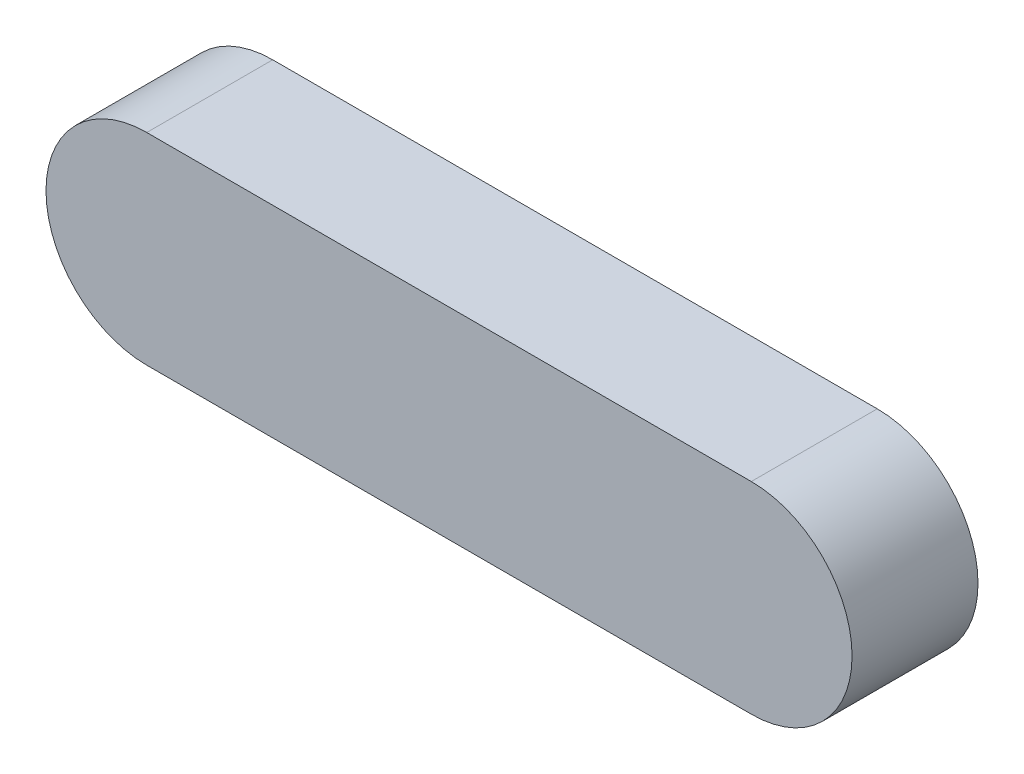
SolidWorks part; units mm, degrees
ref_plane "Front Plane" through (0, 0, 0) normal (0, 0, 1) x (1, 0, 0)
ref_plane "Top Plane" through (0, 0, 0) normal (0, 1, 0) x (1, 0, 0)
ref_plane "Right Plane" through (0, 0, 0) normal (1, 0, 0) x (0, 0, -1)
sketch "Sketch1" plane through (0, 0, 0) normal (0, 0, 1) x (1, 0, 0)
  line L0 (-7.6679, 0) -> (40.3321, 0) construction
  line L1 (-7.6679, 8) -> (40.3321, 8)
  line L2 (-7.6679, -8) -> (40.3321, -8)
  arc A0 (-7.6679, 8) -> (-7.6679, -8) centre (-7.6679, 0) ccw
  arc A1 (40.3321, -8) -> (40.3321, 8) centre (40.3321, 0) ccw
  point P3 (16.3321, 0)
  dimension "D1" = 8
  dimension "D2" = 48
extrude "Boss-Extrude1" add sketch "Sketch1" along normal blind 10
